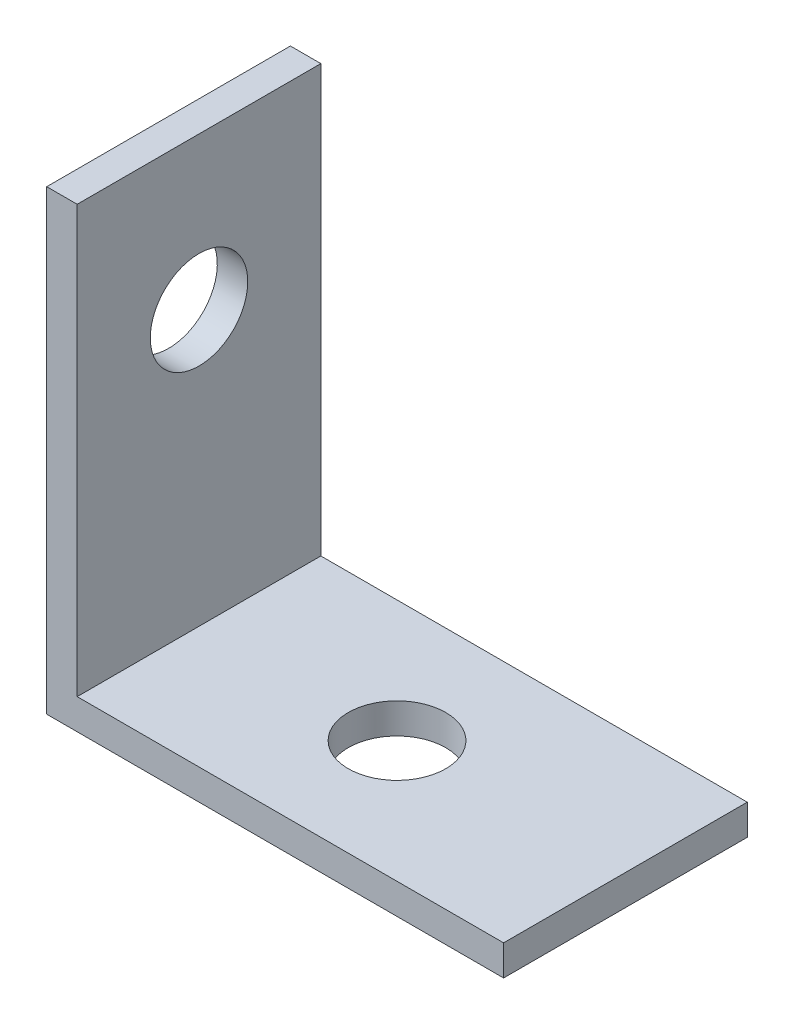
SolidWorks part; units mm, degrees
material "1060 Сплав"
ref_plane "Спереди" through (0, 0, 0) normal (0, 0, 1) x (1, 0, 0)
ref_plane "Сверху" through (0, 0, 0) normal (0, 1, 0) x (1, 0, 0)
ref_plane "Справа" through (0, 0, 0) normal (1, 0, 0) x (0, 0, -1)
sketch "Эскиз1" plane through (0, 0, 0) normal (0, 0, 1) x (1, 0, 0)
  line L0 (0, 0) -> (15, 0)
  line L1 (15, 0) -> (15, 1)
  line L2 (15, 1) -> (1, 1)
  line L3 (1, 1) -> (1, 15)
  line L4 (1, 15) -> (0, 15)
  line L5 (0, 15) -> (0, 0)
  dimension "D1" = 1
  dimension "D2" = 15
extrude "Бобышка-Вытянуть1" add sketch "Эскиз1" along normal blind 8
sketch "Эскиз2" plane through (0, 0, 0) normal (0, -1, 0) x (1, 0, 0)
  line L0 (15, 4) -> (0, 4) construction
  line L1 (15, 8) -> (15, 0) construction
  line L2 (0, 8) -> (0, 0) construction
  circle A0 centre (7.5, 4) radius 1.6
  dimension "D1" = 3.2
sketch "Sketch1" plane through (1, 0, 0) normal (1, 0, 0) x (0, 0, -1)
  circle A0 centre (-4, 10) radius 1.55 construction
  circle A1 centre (-4, 10) radius 1.55 construction
  circle A2 centre (-4, 10) radius 1.6
  dimension "D1" = 3.2
extrude "Cut-Extrude1" cut sketch "Sketch1" against normal through all
extrude "Cut-Extrude2" cut sketch "Эскиз2" against normal through all
